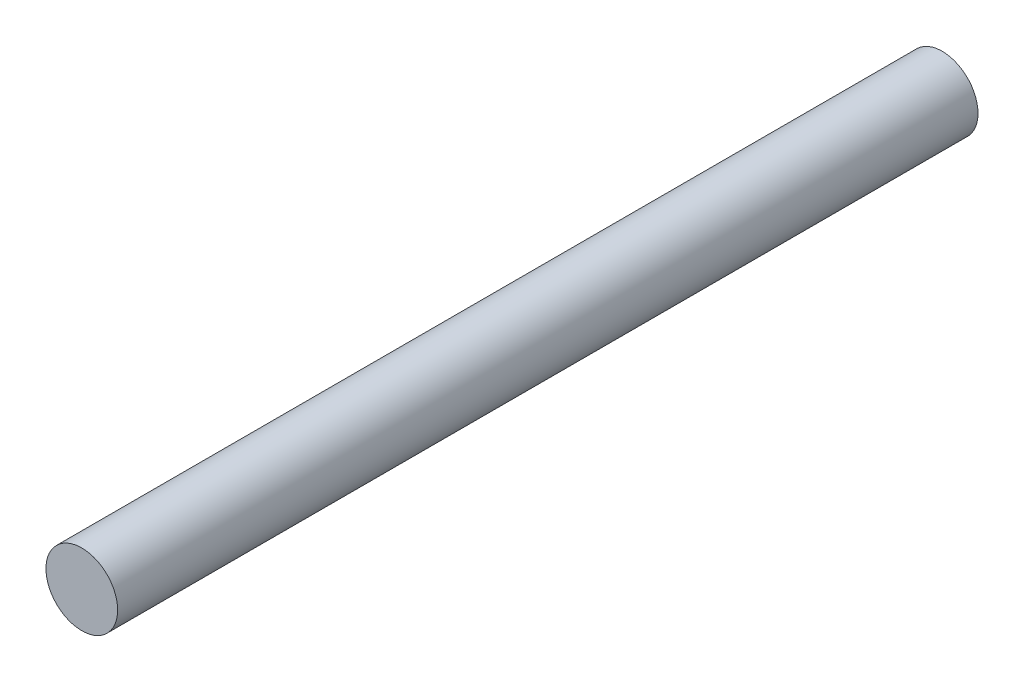
SolidWorks part; units mm, degrees
ref_plane "Front Plane" through (0, 0, 0) normal (0, 0, 1) x (1, 0, 0)
ref_plane "Top Plane" through (0, 0, 0) normal (0, 1, 0) x (1, 0, 0)
ref_plane "Right Plane" through (0, 0, 0) normal (1, 0, 0) x (0, 0, -1)
sketch "Sketch1" plane through (0, 0, 0) normal (0, 0, 1) x (1, 0, 0)
  circle A0 centre (0, 0) radius 5
extrude "Boss-Extrude1" add sketch "Sketch1" along normal blind 120
